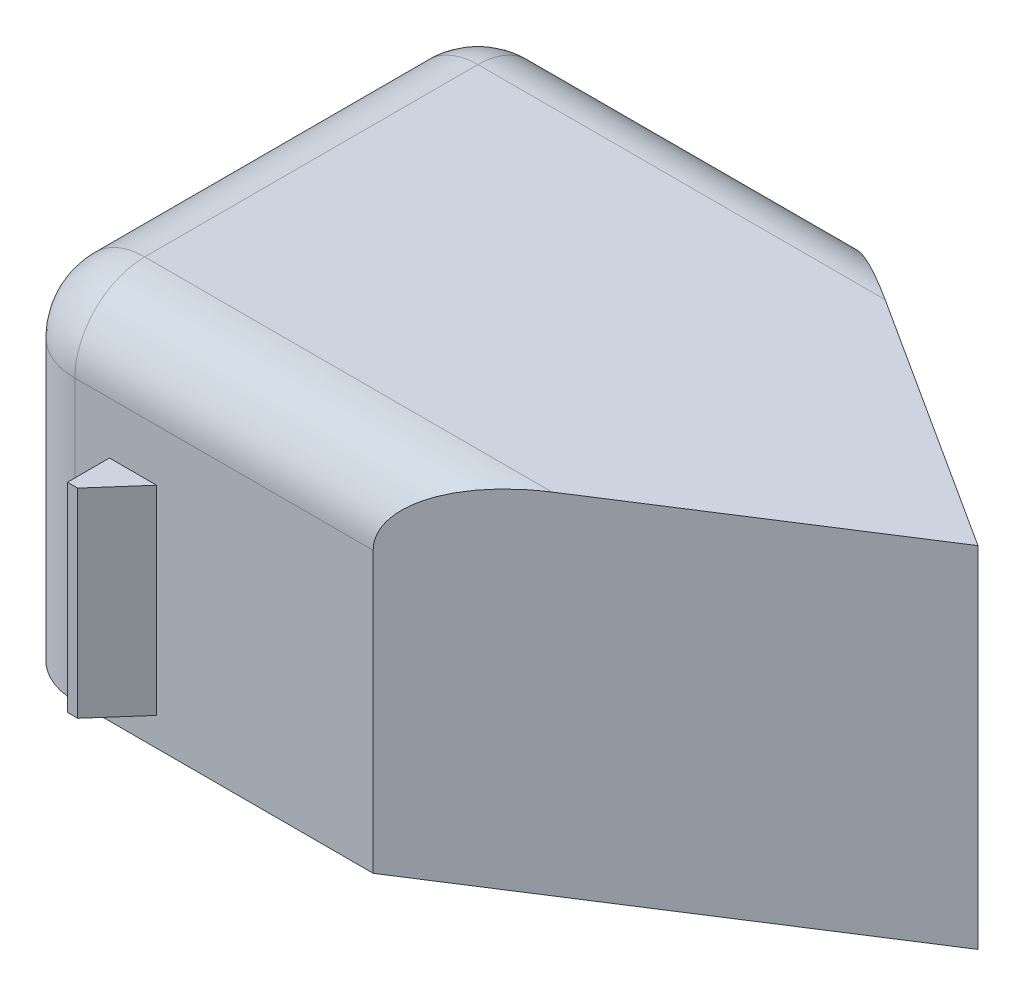
SolidWorks part; units mm, degrees
ref_plane "Front Plane"
ref_plane "Top Plane" through (0, 0, 0) normal (0, 1, 0) x (1, 0, 0)
ref_plane "Right Plane" through (0, 0, 0) normal (1, 0, 0) x (0, 0, -1)
sketch "Sketch1" plane through (0, 0, 0) normal (0, 1, 0) x (1, 0, 0)
  line L0 (0, -33.8164) -> (52.6627, 0)
  line L1 (0, -33.8164) -> (-42.6627, -33.8164)
  line L3 (0, 33.8164) -> (-42.6627, 33.8164)
  line L4 (-52.6627, -23.8164) -> (-52.6627, 23.8164)
  line L5 (26.3314, -16.9082) -> (-52.6627, 33.8164) construction
  line L6 (26.3314, 16.9082) -> (-52.6627, -33.8164) construction
  line L7 (52.6627, 0) -> (0, 33.8164)
  arc A0 (-52.6627, 23.8164) -> (-42.6627, 33.8164) centre (-42.6627, 23.8164) cw
  arc A1 (-52.6627, -23.8164) -> (-42.6627, -33.8164) centre (-42.6627, -23.8164) ccw
  point P0 (0, 0)
  dimension "D1" = 10
  dimension "D2" = 10
extrude "Boss-Extrude1" add sketch "Sketch1" along normal blind 50 contours L3 A0 L4 A1 L1 L0 L7
fillet "Fillet1" radius 10 5 edges at (-21.3314, 50, 33.8164) (-49.7338, 50, 30.8875) (-21.3314, 50, -33.8164) (-49.7338, 50, -30.8875) (-52.6627, 50, 0)
sketch "Sketch2" plane through (0, 0, 33.8164) normal (0, 0, 1) x (1, 0, 0)
  line L1 (-30.9725, 4.0711) -> (-37.7056, 4.0711)
  line L2 (-30.9725, 4.0711) -> (-30.9725, 32.5748)
  line L3 (-30.9725, 32.5748) -> (-37.7056, 32.5748)
  line L4 (-37.7056, 4.0711) -> (-37.7056, 32.5748)
  line L5 (-30.9725, 4.0711) -> (-37.7056, 32.5748) construction
  line L6 (-30.9725, 32.5748) -> (-37.7056, 4.0711) construction
  point P0 (-34.3391, 18.323)
extrude "Boss-Extrude2" add sketch "Sketch2" along normal blind 6
sketch "Sketch3" plane through (0, 4.0711, 0) normal (0, -1, 0) x (-1, 0, 0)
  line L0 (30.9725, -33.8164) -> (36.2468, -39.8164)
  line L1 (37.7056, -39.8164) -> (30.9725, -39.8164) construction
  line L2 (36.2468, -39.8164) -> (30.9725, -39.8164)
  line L3 (30.9725, -39.8164) -> (30.9725, -33.8164)
extrude "Cut-Extrude1" cut sketch "Sketch3" against normal blind 29
